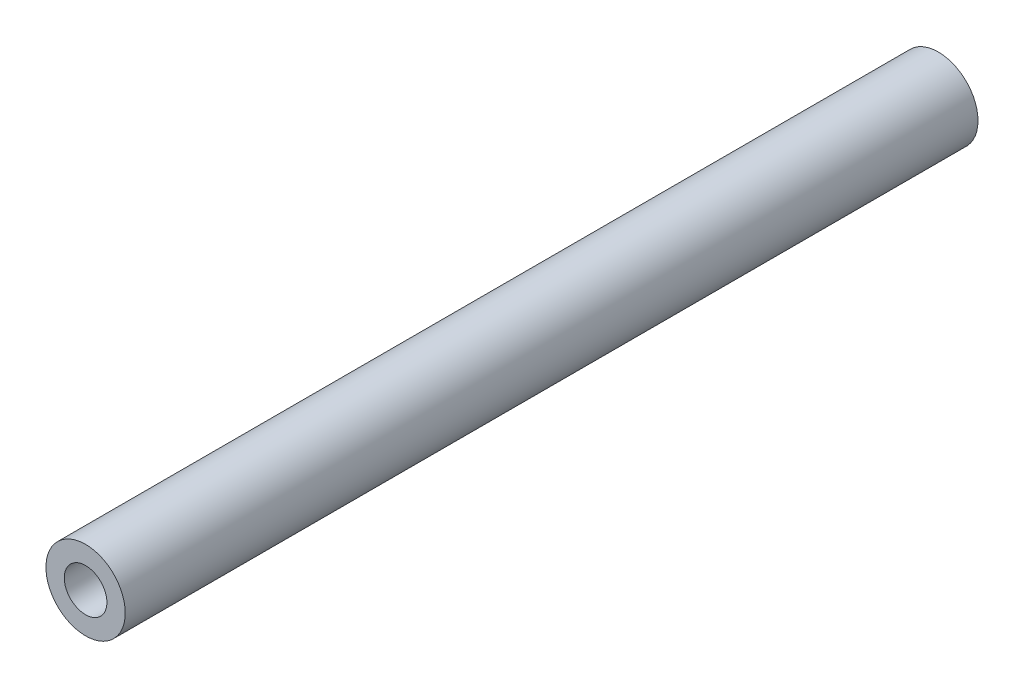
SolidWorks part; units mm, degrees
ref_plane "Front Plane" through (0, 0, 0) normal (0, 0, 1) x (1, 0, 0)
ref_plane "Top Plane" through (0, 0, 0) normal (0, 1, 0) x (1, 0, 0)
ref_plane "Right Plane" through (0, 0, 0) normal (1, 0, 0) x (0, 0, -1)
sketch "Sketch1" plane through (0, 0, 0) normal (0, 0, 1) x (1, 0, 0)
  circle A0 centre (0, 0) radius 1.27
  circle A1 centre (0, 0) radius 2.3622
  dimension "D1" = 2.54
  dimension "D2" = 4.7244
extrude "Boss-Extrude1" add sketch "Sketch1" along normal blind 50.8
